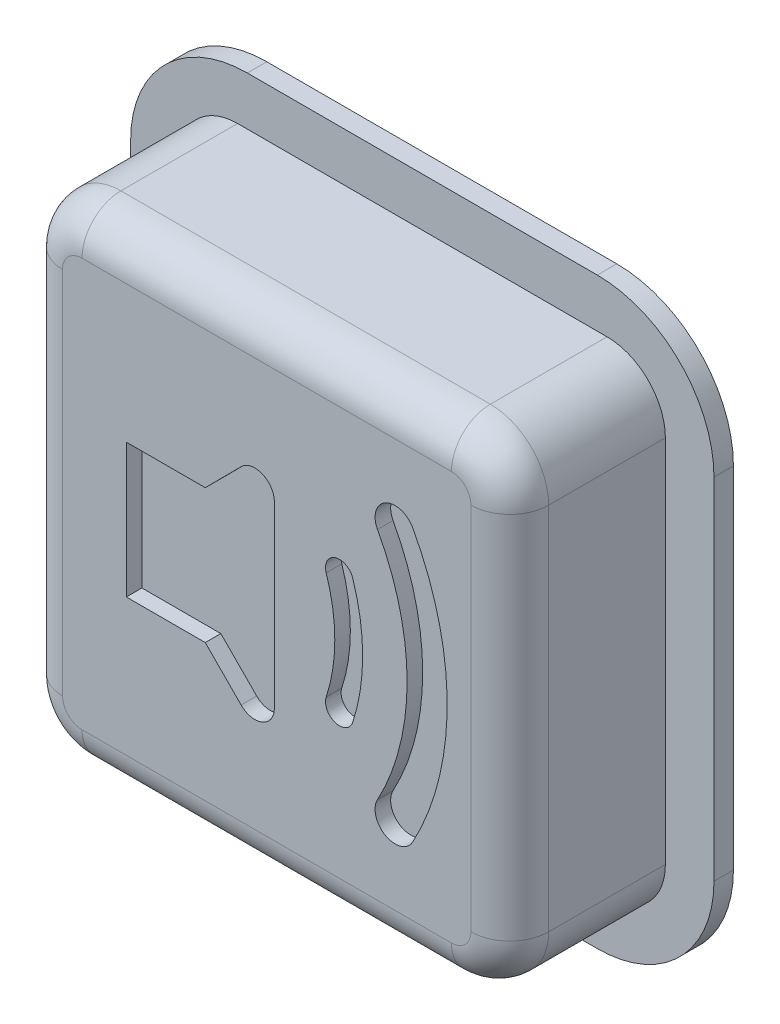
SolidWorks part; units mm, degrees
ref_plane "Front" through (0, 0, 0) normal (0, 0, 1) x (1, 0, 0)
ref_plane "Top" through (0, 0, 0) normal (0, 1, 0) x (1, 0, 0)
ref_plane "Right" through (0, 0, 0) normal (1, 0, 0) x (0, 0, -1)
sketch "Эскиз1" plane through (0, 0, 0) normal (0, 0, 1) x (1, 0, 0)
  line L1 (-6.25, 6.25) -> (6.25, 6.25)
  line L2 (-6.25, 6.25) -> (-6.25, -6.25)
  line L3 (-6.25, -6.25) -> (6.25, -6.25)
  line L4 (6.25, 6.25) -> (6.25, -6.25)
  point P4 (0, 6.25)
  point P5 (6.25, 0)
  dimension "D2" = 12.5
extrude "Основа" add sketch "Эскиз1" along normal blind 4.5
fillet "Скругление1" radius 1.5 4 edges at (6.25, -6.25, 2.25) (6.25, 6.25, 2.25) (-6.25, 6.25, 2.25) (-6.25, -6.25, 2.25)
fillet "Скругление2" radius 1 8 edges at (-5.8107, -5.8107, 4.5) (-6.25, 0, 4.5) (-5.8107, 5.8107, 4.5) (0, 6.25, 4.5) (5.8107, 5.8107, 4.5) (6.25, 0, 4.5) (5.8107, -5.8107, 4.5) (0, -6.25, 4.5)
sketch "Эскиз2" plane through (0, 0, 0) normal (0, 0, -1) x (-1, 0, 0)
  line L0 (6.25, 4.75) -> (6.25, -4.75) construction
  line L1 (-7.5, 7.5) -> (7.5, 7.5)
  line L2 (-7.5, 7.5) -> (-7.5, -7.5)
  line L3 (-7.5, -7.5) -> (7.5, -7.5)
  line L4 (7.5, 7.5) -> (7.5, -7.5)
  point P4 (0, 7.5)
  point P5 (7.5, 0)
  point P9 (6.25, 0)
  dimension "D1" = 15
  dimension "D2" = 15
extrude "Подложка" add sketch "Эскиз2" against normal blind 0.5
fillet "Скругление3" radius 3 4 edges at (7.5, -7.5, 0.25) (-7.5, -7.5, 0.25) (-7.5, 7.5, 0.25) (7.5, 7.5, 0.25)
sketch "Эскиз3" [suppressed] plane through (0, 0, 0) normal (1, 0, 0) x (0, 0, -1)
  line L0 (0, 4.5) -> (0, -4.5) construction
  line L2 (0, 3.5) -> (-1.1038, 3.25)
  line L3 (0, 3.5) -> (0, 0)
  line L4 (-0.5, 4.75) -> (-3.5, 4.75) construction
  line L5 (-3.7, 0) -> (0, 0)
  arc A1 (-1.1038, 3.25) -> (-3.7, 0) centre (-0.3677, 0) ccw
  point P5 (-3.6061, 0)
  point P7 (-0.828, 3.25)
  dimension "D1" = 3.5
  dimension "D2" = 3.7
revolve "Вырез-Повернуть1" [suppressed] cut sketch "Эскиз3" angle 360 about L5
sketch "Эскиз4" plane through (0, 0, 4.5) normal (0, 0, 1) x (1, 0, 0)
  line L3 (-3.6102, 1.724) -> (-3.6102, -1.724)
  line L4 (-3.6102, -1.724) -> (-1.5807, -1.724)
  line L5 (-1.5807, -1.724) -> (0.1954, -3.5154)
  line L6 (0.1954, -3.5154) -> (0.1954, 3.5154)
  line L7 (0.1954, 3.5154) -> (-1.5807, 1.724)
  line L8 (-1.5807, 1.724) -> (-3.6102, 1.724)
  line L9 (0, 0) -> (5.25, 0) construction
  line L10 (5.25, -4.75) -> (5.25, 4.75) construction
  line L11 (-5.25, -4.75) -> (-5.25, 4.75)
  line L12 (-5.25, 4.75) -> (-6.25, 4.75) construction
  line L13 (-4.75, 5.25) -> (4.75, 5.25)
  line L14 (5.25, 4.75) -> (5.25, -4.75)
  line L15 (4.75, -5.25) -> (-4.75, -5.25)
  arc A0 (1.5292, -1.3837) -> (1.5292, 1.3837) centre (-2.7087, 0) ccw
  arc A1 (2.2104, -1.6061) -> (2.2104, 1.6061) centre (-2.7087, 0) ccw
  arc A2 (2.8476, -3.0075) -> (2.8476, 3.0075) centre (-2.7087, 0) ccw
  arc A3 (3.7537, -3.4979) -> (3.7537, 3.4979) centre (-2.7087, 0) ccw
  arc A4 (2.2104, 1.6061) -> (1.5292, 1.3837) centre (1.8698, 1.4949) ccw
  arc A5 (3.7537, 3.4979) -> (2.8476, 3.0075) centre (3.3007, 3.2527) ccw
  arc A6 (3.7537, -3.4979) -> (2.8476, -3.0075) centre (3.3007, -3.2527) cw
  arc A7 (2.2104, -1.6061) -> (1.5292, -1.3837) centre (1.8698, -1.4949) cw
  arc A8 (-5.25, -4.75) -> (-4.75, -5.25) centre (-4.75, -4.75) ccw construction
  arc A9 (-4.75, 5.25) -> (-5.25, 4.75) centre (-4.75, 4.75) ccw construction
  arc A10 (-5.25, 4.75) -> (-4.75, 5.25) centre (-4.75, 4.75) cw
  arc A11 (4.75, 5.25) -> (5.25, 4.75) centre (4.75, 4.75) cw
  arc A12 (5.25, -4.75) -> (4.75, -5.25) centre (4.75, -4.75) cw
  arc A13 (-4.75, -5.25) -> (-5.25, -4.75) centre (-4.75, -4.75) cw
  point P0 (0.1954, 0)
  point P11 (-3.6102, 0)
  point P54 (0, 0)
  dimension "D1" = 4
extrude "Вырез-Вытянуть1" cut sketch "Эскиз4" against normal blind 0.4
fillet "Скругление4" radius 0.5 2 edges at (0.1954, -3.5154, 4.3) (0.1954, 3.5154, 4.3)
